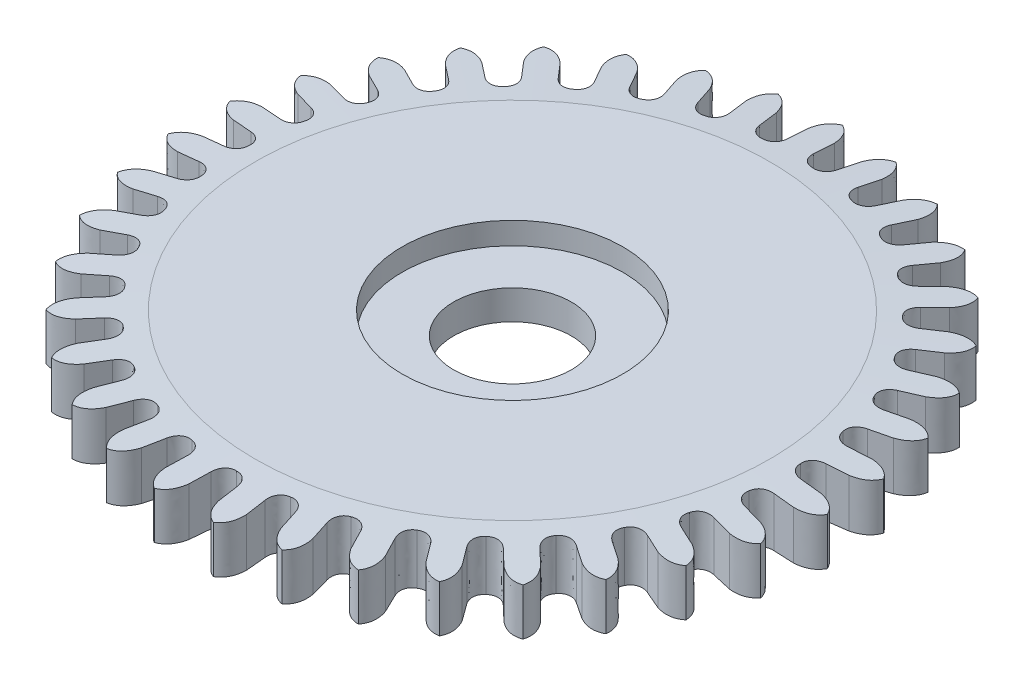
SolidWorks part; units mm, degrees
ref_plane "Alzado" through (0, 0, 0) normal (0, 0, 1) x (1, 0, 0)
ref_plane "Planta" through (0, 0, 0) normal (0, 1, 0) x (1, 0, 0)
ref_plane "Vista lateral" through (0, 0, 0) normal (1, 0, 0) x (0, 0, -1)
sketch "Sketch1" plane through (0, 0, 0) normal (0, 1, 0) x (1, 0, 0)
  circle A0 centre (0, 0) radius 4.485
  dimension "D1" = 8.97
extrude "Boss-Extrude1" add sketch "Sketch1" along normal blind 0.7
chamfer "Chamfer1" distance 0.0614 distance2 0.985 1 edges at (0, 0.7, 4.485)
sketch "Sketch2" plane through (0, 0, 0) normal (0, 1, 0) x (1, 0, 0)
  line L0 (0, -1000) -> (0, 49000) construction
  line L1 (0.176, -999.6664) -> (0.176, 49000.3336) construction
  line L2 (0.0103, 0.1141) -> (4481.9757, 49798.8288) construction
  line L3 (0.176, 4.1993) -> (0.176, 3.9191)
  line L4 (-0.176, 4.1993) -> (-0.176, 3.9191)
  line L5 (0.5766, 4.1633) -> (0.5266, 3.8875)
  line L6 (0.923, 4.1004) -> (0.8729, 3.8246)
  line L7 (1.3108, 3.9934) -> (1.2123, 3.731)
  line L8 (1.6403, 3.8697) -> (1.5418, 3.6073)
  line L9 (2.0027, 3.6952) -> (1.859, 3.4546)
  line L10 (2.3049, 3.5146) -> (2.1612, 3.274)
  line L11 (2.6304, 3.2782) -> (2.446, 3.0671)
  line L12 (2.8954, 3.0466) -> (2.711, 2.8355)
  line L13 (3.1734, 2.7558) -> (2.9543, 2.5811)
  line L14 (3.3929, 2.4806) -> (3.1738, 2.3059)
  line L15 (3.6145, 2.1449) -> (3.3677, 2.0121)
  line L16 (3.7813, 1.8349) -> (3.5345, 1.7021)
  line L17 (3.9394, 1.465) -> (3.6729, 1.3784)
  line L18 (4.0482, 1.1303) -> (3.7816, 1.0437)
  line L19 (4.1377, 0.7381) -> (3.86, 0.7005)
  line L20 (4.1849, 0.3893) -> (3.9072, 0.3517)
  line L21 (4.203, -0.0126) -> (3.923, 0)
  line L22 (4.1872, -0.3642) -> (3.9072, -0.3517)
  line L23 (4.1332, -0.7628) -> (3.86, -0.7005)
  line L24 (4.0549, -1.106) -> (3.7816, -1.0437)
  line L25 (3.9306, -1.4886) -> (3.6728, -1.3784)
  line L26 (3.7922, -1.8123) -> (3.5345, -1.7021)
  line L27 (3.6016, -2.1665) -> (3.3677, -2.0121)
  line L28 (3.4077, -2.4603) -> (3.1738, -2.3059)
  line L29 (3.1569, -2.7748) -> (2.9543, -2.5811)
  line L30 (2.9136, -3.0292) -> (2.711, -2.8355)
  line L31 (2.6107, -3.2939) -> (2.4459, -3.0671)
  line L32 (2.3259, -3.5008) -> (2.1612, -3.274)
  line L33 (1.9806, -3.7071) -> (1.859, -3.4546)
  line L34 (1.6634, -3.8598) -> (1.5418, -3.6073)
  line L35 (1.2868, -4.0012) -> (1.2123, -3.731)
  line L36 (0.9475, -4.0948) -> (0.873, -3.8246)
  line L37 (0.5517, -4.1666) -> (0.5266, -3.8875)
  line L38 (0.2011, -4.1982) -> (0.176, -3.919)
  line L39 (-0.2011, -4.1982) -> (-0.176, -3.919)
  line L40 (-0.5517, -4.1666) -> (-0.5266, -3.8875)
  line L41 (-0.9475, -4.0948) -> (-0.873, -3.8246)
  line L42 (-1.2868, -4.0012) -> (-1.2123, -3.731)
  line L43 (-1.6634, -3.8598) -> (-1.5418, -3.6073)
  line L44 (-1.9806, -3.7071) -> (-1.859, -3.4546)
  line L45 (-2.3259, -3.5008) -> (-2.1612, -3.274)
  line L46 (-2.6107, -3.2939) -> (-2.4459, -3.0671)
  line L47 (-2.9136, -3.0292) -> (-2.711, -2.8355)
  line L48 (-3.1569, -2.7748) -> (-2.9543, -2.5811)
  line L49 (-3.4077, -2.4603) -> (-3.1738, -2.3059)
  line L50 (-3.6016, -2.1665) -> (-3.3677, -2.0121)
  line L51 (-3.7922, -1.8123) -> (-3.5345, -1.7021)
  line L52 (-3.9306, -1.4886) -> (-3.6728, -1.3784)
  line L53 (-4.0549, -1.106) -> (-3.7816, -1.0437)
  line L54 (-4.1332, -0.7628) -> (-3.86, -0.7005)
  line L55 (-4.1872, -0.3642) -> (-3.9072, -0.3517)
  line L56 (-4.203, -0.0126) -> (-3.923, 0)
  line L57 (-4.1849, 0.3893) -> (-3.9072, 0.3517)
  line L58 (-4.1377, 0.7381) -> (-3.86, 0.7005)
  line L59 (-4.0482, 1.1303) -> (-3.7816, 1.0437)
  line L60 (-3.9394, 1.465) -> (-3.6729, 1.3784)
  line L61 (-3.7813, 1.8349) -> (-3.5345, 1.7021)
  line L62 (-3.6145, 2.1449) -> (-3.3677, 2.0121)
  line L63 (-3.3929, 2.4806) -> (-3.1738, 2.3059)
  line L64 (-3.1734, 2.7558) -> (-2.9543, 2.5811)
  line L65 (-2.8954, 3.0466) -> (-2.711, 2.8355)
  line L66 (-2.6304, 3.2782) -> (-2.446, 3.0671)
  line L67 (-2.3049, 3.5146) -> (-2.1612, 3.274)
  line L68 (-2.0027, 3.6952) -> (-1.859, 3.4546)
  line L69 (-1.6403, 3.8697) -> (-1.5418, 3.6073)
  line L70 (-1.3108, 3.9934) -> (-1.2123, 3.731)
  line L71 (-0.923, 4.1004) -> (-0.8729, 3.8246)
  line L72 (-0.5766, 4.1633) -> (-0.5266, 3.8875)
  circle A0 centre (0, 0) radius 3.75 construction
  circle A1 centre (0, 0) radius 4.485
  circle A2 centre (0, 0) radius 4.485 construction
  circle A3 centre (0, 0) radius 4.203 construction
  circle A4 centre (0, 0) radius 3.923 construction
  parabola Q0 (0, 4.485) -> (0.176, 4.1993) focus (-0.023, 4.334) apex (0.0724, 4.4354)
  parabola Q1 (0, 4.485) -> (-0.176, 4.1993) focus (0.023, 4.334) apex (-0.0724, 4.4354)
  parabola Q2 (0.8008, 4.4129) -> (0.5766, 4.1633) focus (0.7965, 4.2602) apex (0.7207, 4.3771)
  parabola Q3 (0.8008, 4.4129) -> (0.923, 4.1004) focus (0.7512, 4.2685) apex (0.8632, 4.3512)
  parabola Q4 (1.5759, 4.199) -> (1.3108, 3.9934) focus (1.5444, 4.0496) apex (1.4907, 4.1781)
  parabola Q5 (1.5759, 4.199) -> (1.6403, 3.8697) focus (1.5013, 4.0657) apex (1.6263, 4.1272)
  parabola Q6 (2.3004, 3.8501) -> (2.0027, 3.6952) focus (2.2426, 3.7087) apex (2.2128, 3.8447)
  parabola Q7 (2.3004, 3.8501) -> (2.3049, 3.5146) focus (2.2032, 3.7323) apex (2.3371, 3.7705)
  parabola Q8 (2.9509, 3.3775) -> (2.6304, 3.2782) focus (2.8688, 3.2487) apex (2.8637, 3.3878)
  parabola Q9 (2.9509, 3.3775) -> (2.8954, 3.0466) focus (2.8342, 3.2789) apex (2.9728, 3.2926)
  parabola Q10 (3.5065, 2.7964) -> (3.1734, 2.7558) focus (3.4028, 2.6842) apex (3.4226, 2.8221)
  parabola Q11 (3.5065, 2.7964) -> (3.3929, 2.4806) focus (3.3741, 2.7202) apex (3.5129, 2.7089)
  parabola Q12 (3.9495, 2.1253) -> (3.6145, 2.1449) focus (3.8274, 2.0335) apex (3.8715, 2.1656)
  parabola Q13 (3.9495, 2.1253) -> (3.7813, 1.8349) focus (3.8056, 2.074) apex (3.9401, 2.0381)
  parabola Q14 (4.2655, 1.3859) -> (3.9394, 1.465) focus (4.129, 1.3174) apex (4.196, 1.4395)
  parabola Q15 (4.2655, 1.3859) -> (4.0482, 1.1303) focus (4.1148, 1.3612) apex (4.2407, 1.3018)
  parabola Q16 (4.4444, 0.602) -> (4.1377, 0.7381) focus (4.2979, 0.559) apex (4.3856, 0.6671)
  parabola Q17 (4.4444, 0.602) -> (4.1849, 0.3893) focus (4.2917, 0.6046) apex (4.405, 0.5236)
  parabola Q18 (4.4805, -0.2012) -> (4.203, -0.0126) focus (4.3286, -0.2174) apex (4.4342, -0.1267)
  parabola Q19 (4.4805, -0.2012) -> (4.1872, -0.3642) focus (4.3307, -0.1715) apex (4.4277, -0.2713)
  parabola Q20 (4.3726, -0.998) -> (4.1332, -0.7628) focus (4.2202, -0.9868) apex (4.3403, -0.9164)
  parabola Q21 (4.3726, -0.998) -> (4.0549, -1.106) focus (4.2305, -0.942) apex (4.3081, -1.0576)
  parabola Q22 (4.1241, -1.7627) -> (3.9306, -1.4886) focus (3.9762, -1.7245) apex (4.107, -1.6767)
  parabola Q23 (4.1241, -1.7627) -> (3.7922, -1.8123) focus (3.9943, -1.6822) apex (4.0501, -1.8098)
  parabola Q24 (3.7431, -2.4708) -> (3.6016, -2.1665) focus (3.6044, -2.4068) apex (3.7416, -2.3831)
  parabola Q25 (3.7431, -2.4708) -> (3.4077, -2.4603) focus (3.6297, -2.3684) apex (3.6618, -2.5039)
  parabola Q26 (3.2417, -3.0994) -> (3.1569, -2.7748) focus (3.1167, -3.0117) apex (3.2559, -3.0128)
  parabola Q27 (3.2417, -3.0994) -> (2.9136, -3.0292) focus (3.1485, -2.9784) apex (3.1559, -3.1175)
  parabola Q28 (2.6362, -3.6284) -> (2.6107, -3.2939) focus (2.5289, -3.5198) apex (2.6657, -3.5458)
  parabola Q29 (2.6362, -3.6284) -> (2.3259, -3.5008) focus (2.5661, -3.4928) apex (2.5485, -3.6309)
  parabola Q30 (1.946, -4.0408) -> (1.9806, -3.7071) focus (1.8597, -3.9148) apex (1.9897, -3.9648)
  parabola Q31 (1.946, -4.0408) -> (1.6634, -3.8598) focus (1.9012, -3.8948) apex (1.8592, -4.0276)
  parabola Q32 (1.1932, -4.3234) -> (1.2868, -4.0012) focus (1.1308, -4.1839) apex (1.2498, -4.2563)
  parabola Q33 (1.1932, -4.3234) -> (0.9475, -4.0948) focus (1.1752, -4.1717) apex (1.1102, -4.2949)
  parabola Q34 (0.402, -4.4669) -> (0.5517, -4.1666) focus (0.3656, -4.3186) apex (0.4697, -4.4111)
  parabola Q35 (0.402, -4.4669) -> (0.2011, -4.1982) focus (0.4114, -4.3145) apex (0.3255, -4.4241)
  parabola Q36 (-0.402, -4.4669) -> (-0.2011, -4.1982) focus (-0.4114, -4.3145) apex (-0.3255, -4.4241)
  parabola Q37 (-0.402, -4.4669) -> (-0.5517, -4.1666) focus (-0.3656, -4.3186) apex (-0.4697, -4.4111)
  parabola Q38 (-1.1932, -4.3234) -> (-0.9475, -4.0948) focus (-1.1752, -4.1717) apex (-1.1102, -4.2949)
  parabola Q39 (-1.1932, -4.3234) -> (-1.2868, -4.0012) focus (-1.1308, -4.1839) apex (-1.2498, -4.2563)
  parabola Q40 (-1.946, -4.0408) -> (-1.6634, -3.8598) focus (-1.9012, -3.8948) apex (-1.8592, -4.0276)
  parabola Q41 (-1.946, -4.0408) -> (-1.9806, -3.7071) focus (-1.8597, -3.9148) apex (-1.9897, -3.9648)
  parabola Q42 (-2.6362, -3.6284) -> (-2.3259, -3.5008) focus (-2.5661, -3.4928) apex (-2.5485, -3.6309)
  parabola Q43 (-2.6362, -3.6284) -> (-2.6107, -3.2939) focus (-2.5289, -3.5198) apex (-2.6657, -3.5458)
  parabola Q44 (-3.2417, -3.0994) -> (-2.9136, -3.0292) focus (-3.1485, -2.9784) apex (-3.1559, -3.1175)
  parabola Q45 (-3.2417, -3.0994) -> (-3.1569, -2.7748) focus (-3.1167, -3.0117) apex (-3.2559, -3.0128)
  parabola Q46 (-3.7431, -2.4708) -> (-3.4077, -2.4603) focus (-3.6297, -2.3684) apex (-3.6618, -2.5039)
  parabola Q47 (-3.7431, -2.4708) -> (-3.6016, -2.1665) focus (-3.6044, -2.4068) apex (-3.7416, -2.3831)
  parabola Q48 (-4.1241, -1.7627) -> (-3.7922, -1.8123) focus (-3.9943, -1.6822) apex (-4.0501, -1.8098)
  parabola Q49 (-4.1241, -1.7627) -> (-3.9306, -1.4886) focus (-3.9762, -1.7245) apex (-4.107, -1.6767)
  parabola Q50 (-4.3726, -0.998) -> (-4.0549, -1.106) focus (-4.2305, -0.942) apex (-4.3081, -1.0576)
  parabola Q51 (-4.3726, -0.998) -> (-4.1332, -0.7628) focus (-4.2202, -0.9868) apex (-4.3403, -0.9164)
  parabola Q52 (-4.4805, -0.2012) -> (-4.1872, -0.3642) focus (-4.3307, -0.1715) apex (-4.4277, -0.2713)
  parabola Q53 (-4.4805, -0.2012) -> (-4.203, -0.0126) focus (-4.3286, -0.2174) apex (-4.4342, -0.1267)
  parabola Q54 (-4.4444, 0.602) -> (-4.1849, 0.3893) focus (-4.2917, 0.6046) apex (-4.405, 0.5236)
  parabola Q55 (-4.4444, 0.602) -> (-4.1377, 0.7381) focus (-4.2979, 0.559) apex (-4.3856, 0.6671)
  parabola Q56 (-4.2655, 1.3859) -> (-4.0482, 1.1303) focus (-4.1148, 1.3612) apex (-4.2407, 1.3018)
  parabola Q57 (-4.2655, 1.3859) -> (-3.9394, 1.465) focus (-4.129, 1.3174) apex (-4.196, 1.4395)
  parabola Q58 (-3.9495, 2.1253) -> (-3.7813, 1.8349) focus (-3.8056, 2.074) apex (-3.9401, 2.0381)
  parabola Q59 (-3.9495, 2.1253) -> (-3.6145, 2.1449) focus (-3.8274, 2.0335) apex (-3.8715, 2.1656)
  parabola Q60 (-3.5065, 2.7964) -> (-3.3929, 2.4806) focus (-3.3741, 2.7202) apex (-3.5129, 2.7089)
  parabola Q61 (-3.5065, 2.7964) -> (-3.1734, 2.7558) focus (-3.4028, 2.6842) apex (-3.4226, 2.8221)
  parabola Q62 (-2.9509, 3.3775) -> (-2.8954, 3.0466) focus (-2.8342, 3.2789) apex (-2.9728, 3.2926)
  parabola Q63 (-2.9509, 3.3775) -> (-2.6304, 3.2782) focus (-2.8688, 3.2487) apex (-2.8637, 3.3878)
  parabola Q64 (-2.3004, 3.8501) -> (-2.3049, 3.5146) focus (-2.2032, 3.7323) apex (-2.3371, 3.7705)
  parabola Q65 (-2.3004, 3.8501) -> (-2.0027, 3.6952) focus (-2.2426, 3.7087) apex (-2.2128, 3.8447)
  parabola Q66 (-1.5759, 4.199) -> (-1.6403, 3.8697) focus (-1.5013, 4.0657) apex (-1.6263, 4.1272)
  parabola Q67 (-1.5759, 4.199) -> (-1.3108, 3.9934) focus (-1.5444, 4.0496) apex (-1.4907, 4.1781)
  parabola Q68 (-0.8008, 4.4129) -> (-0.923, 4.1004) focus (-0.7512, 4.2685) apex (-0.8632, 4.3512)
  parabola Q69 (-0.8008, 4.4129) -> (-0.5766, 4.1633) focus (-0.7965, 4.2602) apex (-0.7207, 4.3771)
  spline S0 degree 3 poles (0.176, 3.9191) (0.1752, 3.8364) (0.2221, 3.7413) (0.3361, 3.7349) knots 0 0 0 0 1 1 1 1
  spline S1 degree 3 poles (-0.176, 3.9191) (-0.1752, 3.8364) (-0.2221, 3.7413) (-0.3361, 3.7349) knots 0 0 0 0 1 1 1 1
  spline S2 degree 3 poles (0.5266, 3.8875) (0.5126, 3.8061) (0.4495, 3.7208) (0.3361, 3.7349) knots 0 0 0 0 1 1 1 1
  spline S3 degree 3 poles (0.8729, 3.8246) (0.8574, 3.7435) (0.8866, 3.6415) (0.9976, 3.6149) knots 0 0 0 0 1 1 1 1
  spline S4 degree 3 poles (1.2123, 3.731) (1.184, 3.6534) (1.1066, 3.5808) (0.9976, 3.6149) knots 0 0 0 0 1 1 1 1
  spline S5 degree 3 poles (1.5418, 3.6073) (1.5121, 3.5302) (1.5226, 3.4247) (1.6271, 3.3786) knots 0 0 0 0 1 1 1 1
  spline S6 degree 3 poles (1.859, 3.4546) (1.8173, 3.3833) (1.7282, 3.3257) (1.6271, 3.3786) knots 0 0 0 0 1 1 1 1
  spline S7 degree 3 poles (2.1612, 3.274) (2.1181, 3.2035) (2.1096, 3.0978) (2.2042, 3.0338) knots 0 0 0 0 1 1 1 1
  spline S8 degree 3 poles (2.446, 3.0671) (2.3922, 3.0044) (2.2943, 2.9636) (2.2042, 3.0338) knots 0 0 0 0 1 1 1 1
  spline S9 degree 3 poles (2.711, 2.8355) (2.6561, 2.7738) (2.6288, 2.6713) (2.7105, 2.5915) knots 0 0 0 0 1 1 1 1
  spline S10 degree 3 poles (2.9543, 2.5811) (2.8902, 2.529) (2.7866, 2.5063) (2.7105, 2.5915) knots 0 0 0 0 1 1 1 1
  spline S11 degree 3 poles (3.1738, 2.3059) (3.1087, 2.255) (3.0636, 2.159) (3.1296, 2.0659) knots 0 0 0 0 1 1 1 1
  spline S12 degree 3 poles (3.3677, 2.0121) (3.2953, 1.9723) (3.1893, 1.9685) (3.1296, 2.0659) knots 0 0 0 0 1 1 1 1
  spline S13 degree 3 poles (3.5345, 1.7021) (3.4614, 1.6637) (3.3998, 1.5773) (3.4482, 1.4738) knots 0 0 0 0 1 1 1 1
  spline S14 degree 3 poles (3.6729, 1.3784) (3.5945, 1.3522) (3.4895, 1.3674) (3.4482, 1.4738) knots 0 0 0 0 1 1 1 1
  spline S15 degree 3 poles (3.7816, 1.0437) (3.7028, 1.0189) (3.6268, 0.9449) (3.656, 0.8345) knots 0 0 0 0 1 1 1 1
  spline S16 degree 3 poles (3.86, 0.7005) (3.7782, 0.6886) (3.6776, 0.7223) (3.656, 0.8345) knots 0 0 0 0 1 1 1 1
  spline S17 degree 3 poles (3.9072, 0.3517) (3.8252, 0.3413) (3.7373, 0.2821) (3.7462, 0.1682) knots 0 0 0 0 1 1 1 1
  spline S18 degree 3 poles (3.923, 0) (3.8404, 0.0029) (3.7475, 0.0541) (3.7462, 0.1682) knots 0 0 0 0 1 1 1 1
  spline S19 degree 3 poles (3.9072, -0.3517) (3.8247, -0.3472) (3.7276, -0.3898) (3.7161, -0.5034) knots 0 0 0 0 1 1 1 1
  spline S20 degree 3 poles (3.86, -0.7005) (3.7792, -0.6829) (3.6969, -0.6159) (3.7161, -0.5034) knots 0 0 0 0 1 1 1 1
  spline S21 degree 3 poles (3.7816, -1.0437) (3.7013, -1.0245) (3.5981, -1.0491) (3.5665, -1.1588) knots 0 0 0 0 1 1 1 1
  spline S22 degree 3 poles (3.6728, -1.3784) (3.5966, -1.3467) (3.5275, -1.2662) (3.5665, -1.1588) knots 0 0 0 0 1 1 1 1
  spline S23 degree 3 poles (3.5345, -1.7021) (3.4588, -1.6689) (3.3529, -1.6747) (3.3022, -1.777) knots 0 0 0 0 1 1 1 1
  spline S24 degree 3 poles (3.3677, -2.0121) (3.2983, -1.9672) (3.2448, -1.8757) (3.3022, -1.777) knots 0 0 0 0 1 1 1 1
  spline S25 degree 3 poles (3.1738, -2.3059) (3.1053, -2.2597) (3, -2.2465) (2.9319, -2.3381) knots 0 0 0 0 1 1 1 1
  spline S26 degree 3 poles (2.9543, -2.5811) (2.8941, -2.5246) (2.8577, -2.4249) (2.9319, -2.3381) knots 0 0 0 0 1 1 1 1
  spline S27 degree 3 poles (2.711, -2.8355) (2.6519, -2.7779) (2.5507, -2.746) (2.4673, -2.824) knots 0 0 0 0 1 1 1 1
  spline S28 degree 3 poles (2.4459, -3.0671) (2.3968, -3.0008) (2.3788, -2.8962) (2.4673, -2.824) knots 0 0 0 0 1 1 1 1
  spline S29 degree 3 poles (2.1612, -3.274) (2.1132, -3.2067) (2.0194, -3.1574) (1.9234, -3.2192) knots 0 0 0 0 1 1 1 1
  spline S30 degree 3 poles (1.859, -3.4546) (1.8224, -3.3805) (1.8234, -3.2744) (1.9234, -3.2192) knots 0 0 0 0 1 1 1 1
  spline S31 degree 3 poles (1.5418, -3.6073) (1.5067, -3.5325) (1.4231, -3.4672) (1.3177, -3.5109) knots 0 0 0 0 1 1 1 1
  spline S32 degree 3 poles (1.2123, -3.731) (1.1895, -3.6516) (1.2095, -3.5474) (1.3177, -3.5109) knots 0 0 0 0 1 1 1 1
  spline S33 degree 3 poles (0.873, -3.8246) (0.8517, -3.7448) (0.7812, -3.6656) (0.6696, -3.6897) knots 0 0 0 0 1 1 1 1
  spline S34 degree 3 poles (0.5266, -3.8875) (0.5184, -3.8053) (0.5566, -3.7063) (0.6696, -3.6897) knots 0 0 0 0 1 1 1 1
  spline S35 degree 3 poles (0.176, -3.919) (0.1694, -3.8367) (0.1141, -3.7462) (0, -3.75) knots 0 0 0 0 1 1 1 1
  spline S36 degree 3 poles (-0.176, -3.919) (-0.1694, -3.8367) (-0.1141, -3.7462) (0, -3.75) knots 0 0 0 0 1 1 1 1
  spline S37 degree 3 poles (-0.5266, -3.8875) (-0.5184, -3.8053) (-0.5566, -3.7063) (-0.6696, -3.6897) knots 0 0 0 0 1 1 1 1
  spline S38 degree 3 poles (-0.873, -3.8246) (-0.8517, -3.7448) (-0.7812, -3.6656) (-0.6696, -3.6897) knots 0 0 0 0 1 1 1 1
  spline S39 degree 3 poles (-1.2123, -3.731) (-1.1895, -3.6516) (-1.2095, -3.5474) (-1.3177, -3.5109) knots 0 0 0 0 1 1 1 1
  spline S40 degree 3 poles (-1.5418, -3.6073) (-1.5067, -3.5325) (-1.4231, -3.4672) (-1.3177, -3.5109) knots 0 0 0 0 1 1 1 1
  spline S41 degree 3 poles (-1.859, -3.4546) (-1.8224, -3.3805) (-1.8234, -3.2744) (-1.9234, -3.2192) knots 0 0 0 0 1 1 1 1
  spline S42 degree 3 poles (-2.1612, -3.274) (-2.1132, -3.2067) (-2.0194, -3.1574) (-1.9234, -3.2192) knots 0 0 0 0 1 1 1 1
  spline S43 degree 3 poles (-2.4459, -3.0671) (-2.3968, -3.0008) (-2.3788, -2.8962) (-2.4673, -2.824) knots 0 0 0 0 1 1 1 1
  spline S44 degree 3 poles (-2.711, -2.8355) (-2.6519, -2.7779) (-2.5507, -2.746) (-2.4673, -2.824) knots 0 0 0 0 1 1 1 1
  spline S45 degree 3 poles (-2.9543, -2.5811) (-2.8941, -2.5246) (-2.8577, -2.4249) (-2.9319, -2.3381) knots 0 0 0 0 1 1 1 1
  spline S46 degree 3 poles (-3.1738, -2.3059) (-3.1053, -2.2597) (-3, -2.2465) (-2.9319, -2.3381) knots 0 0 0 0 1 1 1 1
  spline S47 degree 3 poles (-3.3677, -2.0121) (-3.2983, -1.9672) (-3.2448, -1.8757) (-3.3022, -1.777) knots 0 0 0 0 1 1 1 1
  spline S48 degree 3 poles (-3.5345, -1.7021) (-3.4588, -1.6689) (-3.3529, -1.6747) (-3.3022, -1.777) knots 0 0 0 0 1 1 1 1
  spline S49 degree 3 poles (-3.6728, -1.3784) (-3.5966, -1.3467) (-3.5275, -1.2662) (-3.5665, -1.1588) knots 0 0 0 0 1 1 1 1
  spline S50 degree 3 poles (-3.7816, -1.0437) (-3.7013, -1.0245) (-3.5981, -1.0491) (-3.5665, -1.1588) knots 0 0 0 0 1 1 1 1
  spline S51 degree 3 poles (-3.86, -0.7005) (-3.7792, -0.6829) (-3.6969, -0.6159) (-3.7161, -0.5034) knots 0 0 0 0 1 1 1 1
  spline S52 degree 3 poles (-3.9072, -0.3517) (-3.8247, -0.3472) (-3.7276, -0.3898) (-3.7161, -0.5034) knots 0 0 0 0 1 1 1 1
  spline S53 degree 3 poles (-3.923, 0) (-3.8404, 0.0029) (-3.7475, 0.0541) (-3.7462, 0.1682) knots 0 0 0 0 1 1 1 1
  spline S54 degree 3 poles (-3.9072, 0.3517) (-3.8252, 0.3413) (-3.7373, 0.2821) (-3.7462, 0.1682) knots 0 0 0 0 1 1 1 1
  spline S55 degree 3 poles (-3.86, 0.7005) (-3.7782, 0.6886) (-3.6776, 0.7223) (-3.656, 0.8345) knots 0 0 0 0 1 1 1 1
  spline S56 degree 3 poles (-3.7816, 1.0437) (-3.7028, 1.0189) (-3.6268, 0.9449) (-3.656, 0.8345) knots 0 0 0 0 1 1 1 1
  spline S57 degree 3 poles (-3.6729, 1.3784) (-3.5945, 1.3522) (-3.4895, 1.3674) (-3.4482, 1.4738) knots 0 0 0 0 1 1 1 1
  spline S58 degree 3 poles (-3.5345, 1.7021) (-3.4614, 1.6637) (-3.3998, 1.5773) (-3.4482, 1.4738) knots 0 0 0 0 1 1 1 1
  spline S59 degree 3 poles (-3.3677, 2.0121) (-3.2953, 1.9723) (-3.1893, 1.9685) (-3.1296, 2.0659) knots 0 0 0 0 1 1 1 1
  spline S60 degree 3 poles (-3.1738, 2.3059) (-3.1087, 2.255) (-3.0636, 2.159) (-3.1296, 2.0659) knots 0 0 0 0 1 1 1 1
  spline S61 degree 3 poles (-2.9543, 2.5811) (-2.8902, 2.529) (-2.7866, 2.5063) (-2.7105, 2.5915) knots 0 0 0 0 1 1 1 1
  spline S62 degree 3 poles (-2.711, 2.8355) (-2.6561, 2.7738) (-2.6288, 2.6713) (-2.7105, 2.5915) knots 0 0 0 0 1 1 1 1
  spline S63 degree 3 poles (-2.446, 3.0671) (-2.3922, 3.0044) (-2.2943, 2.9636) (-2.2042, 3.0338) knots 0 0 0 0 1 1 1 1
  spline S64 degree 3 poles (-2.1612, 3.274) (-2.1181, 3.2035) (-2.1096, 3.0978) (-2.2042, 3.0338) knots 0 0 0 0 1 1 1 1
  spline S65 degree 3 poles (-1.859, 3.4546) (-1.8173, 3.3833) (-1.7282, 3.3257) (-1.6271, 3.3786) knots 0 0 0 0 1 1 1 1
  spline S66 degree 3 poles (-1.5418, 3.6073) (-1.5121, 3.5302) (-1.5226, 3.4247) (-1.6271, 3.3786) knots 0 0 0 0 1 1 1 1
  spline S67 degree 3 poles (-1.2123, 3.731) (-1.184, 3.6534) (-1.1066, 3.5808) (-0.9976, 3.6149) knots 0 0 0 0 1 1 1 1
  spline S68 degree 3 poles (-0.8729, 3.8246) (-0.8574, 3.7435) (-0.8866, 3.6415) (-0.9976, 3.6149) knots 0 0 0 0 1 1 1 1
  spline S69 degree 3 poles (-0.5266, 3.8875) (-0.5126, 3.8061) (-0.4495, 3.7208) (-0.3361, 3.7349) knots 0 0 0 0 1 1 1 1
  point P10 (0, 4.485)
  point P11 (-0.023, 4.334)
  point P12 (0.176, 4.1993)
  point P13 (0.176, 3.9191)
  point P16 (0.3361, 3.7349)
  point P405 (0, 0)
  dimension "D2" = 7.5
  dimension "D3" = 0.282
  dimension "D4" = 0.28
  dimension "D5" = 0.176
  dimension "D6" = 0.151
  dimension "D7" = 0.023
  dimension "D8" = 5.143
  dimension "D1" = 0
  dimension "D9" = 35
extrude "Cut-Extrude1 (35 teeth)" cut sketch "Sketch2" along normal up to next (0.7 mm away) flip side to cut
sketch "Sketch3" plane through (0, 0, 0) normal (0, 1, 0) x (1, 0, 0)
  circle A0 centre (0, 0) radius 0.8
  dimension "D1" = 1.6
extrude "Cut-Extrude2" cut sketch "Sketch3" along normal up to next
sketch "Sketch4" plane through (0, 0.7, 0) normal (0, 1, 0) x (1, 0, 0)
  circle A1 centre (0, 0) radius 1.5
  dimension "D1" = 3
extrude "Cut-Extrude3" cut sketch "Sketch4" against normal blind 0.3
